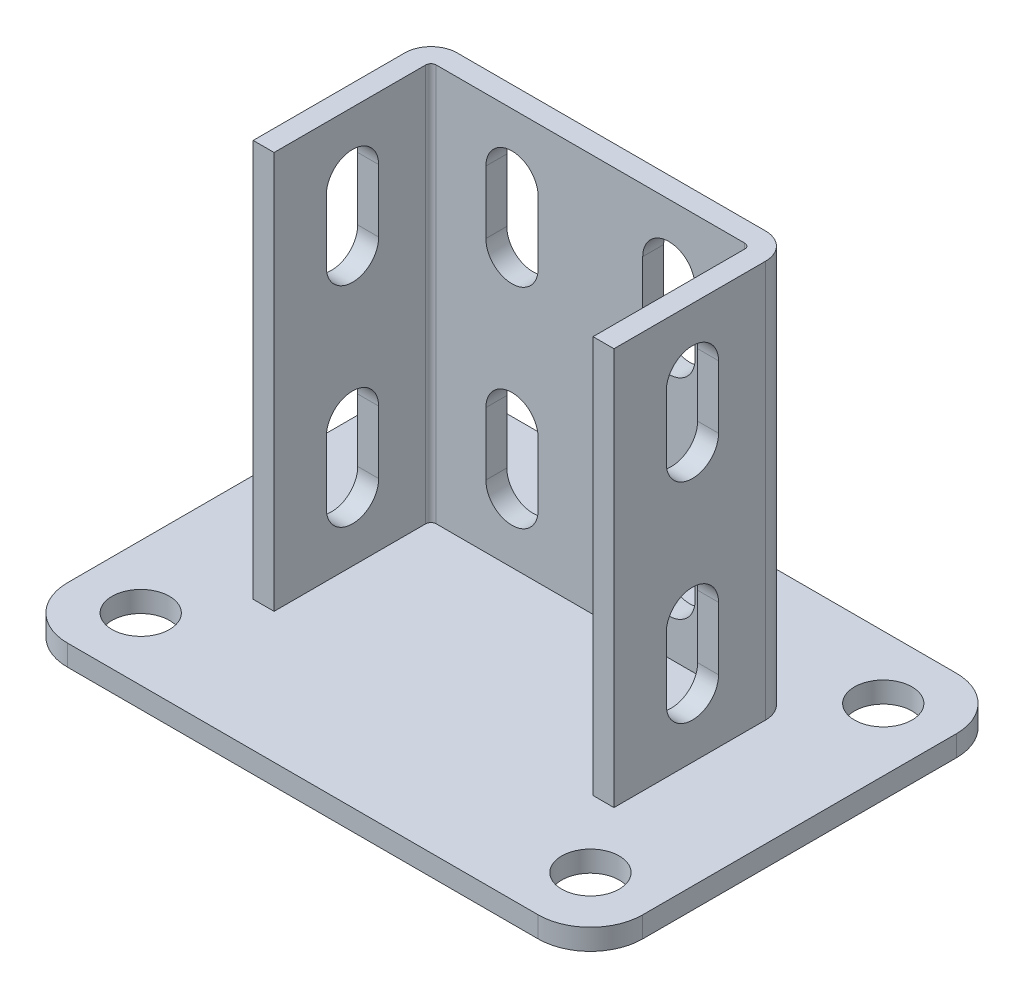
SolidWorks part; units mm, degrees
material "Ст3пс ГОСТ 380-2005"
ref_plane "Спереди" through (0, 0, 0) normal (0, 0, 1) x (1, 0, 0)
ref_plane "Сверху" through (0, 0, 0) normal (0, 1, 0) x (1, 0, 0)
ref_plane "Справа" through (0, 0, 0) normal (1, 0, 0) x (0, 0, -1)
sketch "Эскиз2" plane through (0, 0, 0) normal (0, 1, 0) x (1, 0, 0)
  line L1 (-55, -40) -> (55, -40)
  line L2 (-55, -40) -> (-55, 40)
  line L3 (-55, 40) -> (55, 40)
  line L4 (55, -40) -> (55, 40)
  line L5 (-55, -40) -> (55, 40) construction
  line L6 (-55, 40) -> (55, -40) construction
  point P0 (0, 0)
  dimension "D1" = 80
  dimension "D2" = 110
extrude "Бобышка-Вытянуть1" add sketch "Эскиз2" along normal blind 4
sketch "Эскиз3" plane through (0, 4, 0) normal (0, 1, 0) x (1, 0, 0)
  line L0 (-30.5, -15) -> (-30.5, 15)
  line L1 (-30.5, 15) -> (30.5, 15)
  line L2 (30.5, 15) -> (30.5, -15)
  point P2 (0, 15)
  point P5 (-30.5, 0)
  dimension "D2" = 61
  dimension "D3" = 30
extrude "Вытянуть-Тонкостенный1" add sketch "Эскиз3" along normal offset from surface (76 mm away) 80 thin up to face at (0, 0, 0) thin type one direction reverse wall 4
sketch "Эскиз4" plane through (0, 0, 0) normal (1, 0, 0) x (0, 0, -1)
  line L0 (19, 31.7128) -> (35, 4)
  line L1 (19, 80) -> (19, 4) construction
  line L2 (-40, 4) -> (40, 4) construction
  line L3 (35, 4) -> (19, 4)
  line L4 (19, 4) -> (19, 31.7128)
  line L5 (40, 4) -> (40, 0) construction
  dimension "D1" = 30
  dimension "D2" = 5
extrude "Бобышка-Вытянуть2" add sketch "Эскиз4" along normal mid plane 4
sketch "Эскиз5" plane through (34.5, 0, 0) normal (1, 0, 0) x (0, 0, -1)
  line L0 (0, 68) -> (0, 56) construction
  line L1 (5, 68) -> (5, 56)
  line L2 (-5, 68) -> (-5, 56)
  line L3 (0, 28) -> (0, 16) construction
  line L4 (5, 28) -> (5, 16)
  line L5 (-5, 28) -> (-5, 16)
  line L6 (-15, 80) -> (14, 80) construction
  line L7 (-40, 4) -> (40, 4) construction
  arc A0 (5, 68) -> (-5, 68) centre (0, 68) ccw
  arc A1 (-5, 56) -> (5, 56) centre (0, 56) ccw
  arc A2 (5, 28) -> (-5, 28) centre (0, 28) ccw
  arc A3 (-5, 16) -> (5, 16) centre (0, 16) ccw
  point P3 (0, 62)
  point P8 (0, 22)
  dimension "D2" = 12
  dimension "D4" = 12
  dimension "D1" = 10
  dimension "D3" = 12
extrude "Вырез-Вытянуть1" cut sketch "Эскиз5" against normal through all
sketch "Эскиз6" plane through (0, 4, 0) normal (0, 1, 0) x (1, 0, 0)
  line L0 (-55, 40) -> (-55, -40) construction
  line L1 (43, -28) -> (-43, -28) construction
  line L2 (43, -28) -> (43, 28) construction
  line L3 (43, 28) -> (-43, 28) construction
  line L4 (-43, -28) -> (-43, 28) construction
  line L5 (43, -28) -> (-43, 28) construction
  line L6 (43, 28) -> (-43, -28) construction
  line L7 (55, 40) -> (-55, 40) construction
  circle A0 centre (-43, 28) radius 5.5
  circle A1 centre (-43, -28) radius 5.5
  circle A2 centre (43, 28) radius 5.5
  circle A3 centre (43, -28) radius 5.5
  point P0 (0, 0)
  dimension "D1" = 11
  dimension "D2" = 12
  dimension "D3" = 12
extrude "Вырез-Вытянуть2" cut sketch "Эскиз6" against normal through all
fillet "Скругление1" radius 10 4 edges at (55, 2, 40) (-55, 2, 40) (-55, 2, -40) (55, 2, -40)
sketch "Эскиз8" plane through (0, 0, -19) normal (0, 0, -1) x (-1, 0, 0)
  line L0 (-15, 68) -> (-15, 56) construction
  line L1 (-10, 68) -> (-10, 56)
  line L2 (-20, 68) -> (-20, 56)
  line L3 (-15, 28) -> (-15, 16) construction
  line L4 (-10, 28) -> (-10, 16)
  line L5 (-20, 28) -> (-20, 16)
  line L6 (-29.5, 80) -> (29.5, 80) construction
  line L7 (-45, 4) -> (45, 4) construction
  line L8 (0, 0) -> (0, 80) construction
  line L9 (-45, 0) -> (45, 0) construction
  line L10 (15, 68) -> (15, 56) construction
  line L11 (10, 68) -> (10, 56)
  line L12 (20, 68) -> (20, 56)
  line L13 (15, 28) -> (15, 16) construction
  line L14 (10, 28) -> (10, 16)
  line L15 (20, 28) -> (20, 16)
  arc A0 (-10, 68) -> (-20, 68) centre (-15, 68) ccw
  arc A1 (-20, 56) -> (-10, 56) centre (-15, 56) ccw
  arc A2 (-10, 28) -> (-20, 28) centre (-15, 28) ccw
  arc A3 (-20, 16) -> (-10, 16) centre (-15, 16) ccw
  arc A4 (10, 68) -> (20, 68) centre (15, 68) cw
  arc A5 (20, 56) -> (10, 56) centre (15, 56) cw
  arc A6 (10, 28) -> (20, 28) centre (15, 28) cw
  arc A7 (20, 16) -> (10, 16) centre (15, 16) cw
  point P2 (-15, 62)
  point P7 (-15, 22)
  point P24 (15, 62)
  point P31 (15, 22)
  dimension "D3" = 12
  dimension "D4" = 12
  dimension "D1" = 10
  dimension "D2" = 12
  dimension "D5" = 20
extrude "Вырез-Вытянуть3" cut sketch "Эскиз8" against normal up to next
